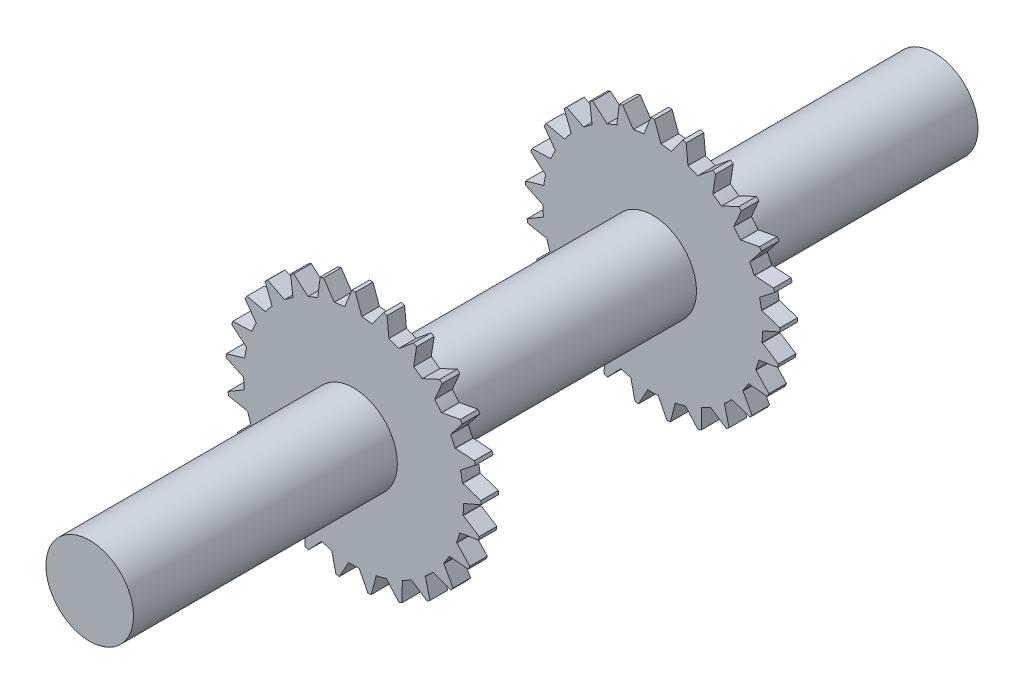
SolidWorks part; units mm, degrees
ref_plane "Front Plane" through (0, 0, 0) normal (0, 0, 1) x (1, 0, 0)
ref_plane "Top Plane" through (0, 0, 0) normal (0, 1, 0) x (1, 0, 0)
ref_plane "Right Plane" through (0, 0, 0) normal (1, 0, 0) x (0, 0, -1)
sketch "Sketch1" plane through (0, 0, 0) normal (0, 0, 1) x (1, 0, 0)
  circle A0 centre (0, 0) radius 24.875
  dimension "D1" = 49.75
extrude "Boss-Extrude1" add sketch "Sketch1" along normal blind 480
ref_plane "Plane1" through (0, 0, 330) normal (0, 0, 1) x (1, 0, 0)
sketch "Sketch2" plane through (0, 0, 330) normal (0, 0, 1) x (1, 0, 0)
  circle A0 centre (0, 0) radius 62.5
  dimension "D1" = 125
extrude "Boss-Extrude2" add sketch "Sketch2" against normal blind 10
sketch "Sketch4" plane through (0, 0, 330) normal (0, 0, 1) x (1, 0, 0)
  line L0 (-5, 62.5) -> (-1, 72.5)
  line L1 (-1, 72.5) -> (1, 72.5)
  line L2 (-5, 62.5) -> (-5, 52.5)
  line L3 (-5, 52.5) -> (5, 52.5)
  line L4 (5, 61.4422) -> (5, 52.5)
  line L5 (-2.7778, 68.0556) -> (5, 52.5) construction
  line L6 (-5, 52.5) -> (2.6791, 67.8582) construction
  line L7 (5, 61.4422) -> (1, 72.5)
  circle A0 centre (0, 0) radius 62.5 construction
  point P0 (0, 62.5)
  dimension "D1" = 10
  dimension "D2" = 1
  dimension "D3" = 5
  dimension "D4" = 1
  dimension "D5" = 52.5
  dimension "D6" = 61.4422
  dimension "D8" = 72.5
extrude "Boss-Extrude3" add sketch "Sketch4" against normal blind 10
pattern_circular "CirPattern2" count 25 over 360 about axis through (0, 0, 0) along (0, 0, 1) of "Boss-Extrude3"
ref_plane "Plane2" through (0, 0, 240) normal (0, 0, 1) x (1, 0, 0)
mirror "Mirror1" about plane through (0, 0, 240) normal (0, 0, 1) of "CirPattern2", "Boss-Extrude3", "Boss-Extrude2"
